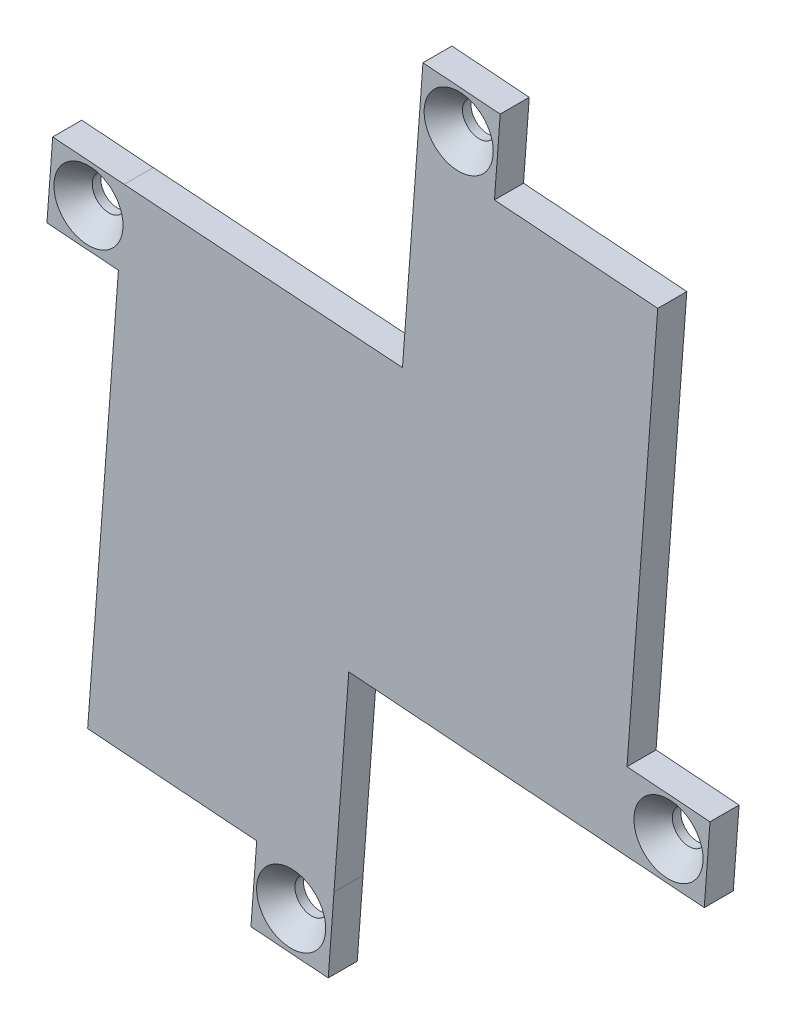
SolidWorks part; units mm, degrees
material "ABS"
ref_plane "Front Plane" through (0, 0, 0) normal (0, 0, 1) x (1, 0, 0)
ref_plane "Top Plane" through (0, 0, 0) normal (0, 1, 0) x (1, 0, 0)
ref_plane "Right Plane" through (0, 0, 0) normal (1, 0, 0) x (0, 0, -1)
sketch "Sketch1" plane through (0, 0, 0) normal (0, 0, 1) x (1, 0, 0)
  line L0 (-32.5898, 17.6165) -> (-25.2094, 17.0659)
  line L1 (-32.5898, 17.6165) -> (-33.185, 9.6387)
  line L2 (-33.185, 9.6387) -> (-25.8046, 9.088)
  line L3 (5.0372, 35.3785) -> (5.6324, 43.3564)
  line L4 (-25.8046, 9.088) -> (-28.9809, -33.4811)
  line L5 (-28.9809, -33.4811) -> (-11.5294, -34.7833)
  line L6 (-11.5294, -34.7833) -> (-12.1246, -42.7611)
  line L7 (-12.1246, -42.7611) -> (-4.1468, -43.3564)
  line L8 (-4.1468, -43.3564) -> (-3.5515, -35.3785)
  line L9 (-3.5515, -35.3785) -> (-2.0253, -14.923)
  line L10 (-2.0253, -14.923) -> (34.6728, -17.6611) construction
  line L11 (-26.8594, -5.0477) -> (-970.5305, 65.3643) construction
  line L12 (35.2681, -9.6833) -> (26.6974, -9.0438) construction
  line L14 (26.6974, -9.0438) -> (29.8736, 33.5254)
  line L15 (29.8736, 33.5254) -> (13.015, 34.7833)
  line L16 (13.015, 34.7833) -> (13.6103, 42.7611)
  line L17 (13.6103, 42.7611) -> (5.6324, 43.3564)
  line L18 (5.0372, 35.3785) -> (3.52, 15.0448)
  line L19 (3.52, 15.0448) -> (-32.5898, 17.6165)
  line L20 (-33.185, 9.6387) -> (-25.8046, 9.088)
  line L22 (3.52, 15.0448) -> (-25.2094, 17.0659)
  line L23 (31.0992, -17.3945) -> (34.0745, -17.6165) construction
  line L24 (34.0745, -17.6165) -> (34.6728, -17.6611)
  line L25 (26.6974, -9.0438) -> (33.8615, -9.5783) construction
  line L26 (34.6728, -17.6611) -> (35.2681, -9.6833)
  line L27 (35.2681, -9.6833) -> (26.6974, -9.0438)
  line L28 (34.6728, -17.6611) -> (-2.0253, -14.923)
extrude "Boss-Extrude1" add sketch "Sketch1" along normal blind 3
hole_wizard "CSK for #5 Flat Head Socket Cap Screw1" positions "Sketch3" profile "Sketch2" countersink size "#5" standard "ANSI Inch" end condition through all
sketch "Sketch3" plane through (0, 0, 3) normal (0, 0, 1) x (1, 0, 0)
  line L0 (-32.5898, 17.6165) -> (-33.185, 9.6387) construction
  line L2 (34.6728, -17.6611) -> (-2.0253, -14.923) construction
  line L5 (-32.5898, 17.6165) -> (-25.2094, 17.0659) construction
  line L6 (5.0372, 35.3785) -> (5.6324, 43.3564) construction
  line L7 (13.6103, 42.7611) -> (5.6324, 43.3564) construction
  line L8 (34.6728, -17.6611) -> (35.2681, -9.6833) construction
  line L10 (-12.1246, -42.7611) -> (-4.1468, -43.3564) construction
  point P0 (-7.9734, -39.0597)
  point P2 (-28.8985, 13.33)
  point P4 (9.3237, 39.0698)
  point P6 (30.9816, -13.3746)
  dimension "D1" = 4
  dimension "D2" = 4
  dimension "D3" = 4
  dimension "D4" = 4
  dimension "D5" = 4
  dimension "D6" = 4
  dimension "D7" = 4
sketch "Sketch2" plane through (-7.9734, -39.0597, 3) normal (1, 0, 0) x (0, -1, 0)
  line L0 (0, 0) -> (0, 3)
  line L1 (0, 3) -> (1.7272, 3)
  line L2 (1.7272, 3) -> (1.7272, 2.1184)
  line L3 (1.7272, 2.1184) -> (3.5687, 0)
  line L5 (3.5687, 0) -> (0, 0)
  line L6 (-1.7272, 2.1184) -> (-3.5687, 0) construction
  line L11 (0, -6.35) -> (0, 107.95) construction
  dimension "Thru Hole Dia." = 3.4544
  dimension "Thru Hole Depth" = 3
  dimension "Near C'Sink Dia." = 7.1374
  dimension "Near C'Sink Angle" = 82
